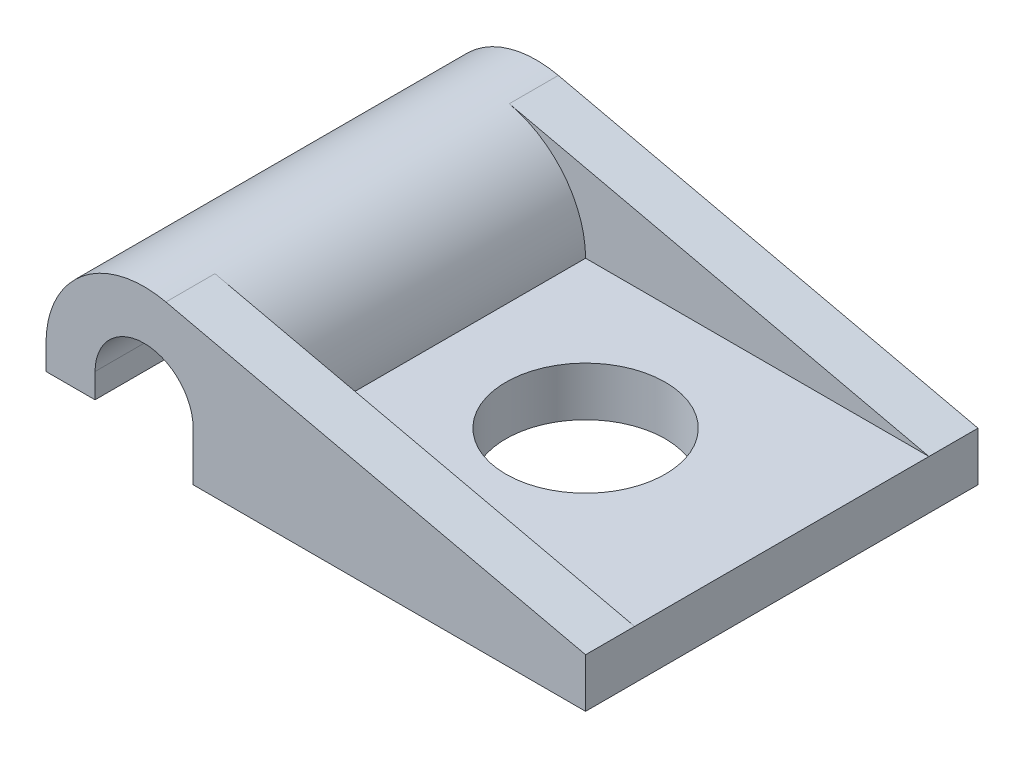
SolidWorks part; units mm, degrees
material "PVC 0.007 Plasticized"
ref_plane "Front" through (0, 0, 0) normal (0, 0, 1) x (1, 0, 0)
ref_plane "Top" through (0, 0, 0) normal (0, 1, 0) x (1, 0, 0)
ref_plane "Right" through (0, 0, 0) normal (1, 0, 0) x (0, 0, -1)
sketch "Sketch1" plane through (0, 0, 0) normal (0, 0, 1) x (1, 0, 0)
  line L11 (0, 14.2875) -> (0, 21.0796) construction
  line L12 (3.175, 1.5875) -> (3.175, 4.1203) construction
  line L13 (14.2875, 1.5875) -> (3.175, 1.5875) construction
  line L14 (-3.175, 0.7937) -> (-3.175, 1.5875)
  line L15 (-1.5875, 0.7937) -> (-3.175, 0.7937)
  line L16 (14.2875, 1.5875) -> (0.7056, 4.6831)
  line L17 (14.2875, 0) -> (14.2875, 1.5875)
  line L18 (1.5875, 0) -> (14.2875, 0)
  line L19 (1.5875, 1.5875) -> (1.5875, 0)
  line L20 (-1.5875, 1.5875) -> (-1.5875, 0.7937)
  arc A0 (1.5875, 1.5875) -> (-1.5875, 1.5875) centre (0, 1.5875) ccw
  arc A5 (-3.175, 1.5875) -> (0.7056, 4.6831) centre (0, 1.5875) cw
  point P2 (1.5181, 2.0516)
  point P13 (4.1275, 1.5875)
  point P41 (7.9375, 0)
  dimension "D1" = 0.7937
  dimension "ID" = 3.175
  dimension "Center to Center" = 7.9375
  dimension "Thickness" = 1.5875
extrude "Boss-Extrude1" add sketch "Sketch1" along normal mid plane 12.7
sketch "Sketch4" plane through (0, 0, 0) normal (0, 1, 0) x (1, 0, 0)
  line L1 (3.175, 4.7625) -> (14.2875, 4.7625)
  line L2 (3.175, 4.7625) -> (3.175, -4.7625)
  line L3 (3.175, -4.7625) -> (14.2875, -4.7625)
  line L4 (14.2875, 4.7625) -> (14.2875, -4.7625)
  line L7 (14.2875, -6.35) -> (14.2875, 6.35) construction
  line L8 (1.5875, 6.35) -> (14.2875, 6.35) construction
  point P6 (14.2875, 0)
  dimension "D1" = 1.5875
extrude "Cut-Extrude3" cut sketch "Sketch4" along normal through all from vertex at 1.5875 starting at point (14.2875, 1.5875, 0)
sketch "Sketch5" plane through (0, 0, 0) normal (0, 0, 1) x (1, 0, 0)
  line L0 (3.175, 1.5875) -> (3.175, 4.1203) construction
  line L1 (3.175, 1.5875) -> (3.175, 4.1203)
  line L3 (14.2875, 1.5875) -> (0.7056, 4.6831) construction
  line L4 (3.175, 4.1203) -> (0.7056, 4.6831)
  arc A1 (0.7056, 4.6831) -> (-3.175, 1.5875) centre (0, 1.5875) ccw construction
  arc A2 (3.175, 1.5875) -> (0.7056, 4.6831) centre (0, 1.5875) ccw
extrude "Cut-Extrude4" cut sketch "Sketch5" along normal up to surface and the other way up to surface up to face at (6.8792, 2.4318, 4.7625) other way up to face at (6.8792, 2.4318, -4.7625)
sketch "Sketch3" plane through (0, 0, 0) normal (0, 1, 0) x (1, 0, 0)
  circle A0 centre (7.9375, 0) radius 2.5797
  dimension "Mounting Hole Dia" = 5.1594
extrude "Cut-Extrude2" cut sketch "Sketch3" along normal blind 2.54
sketch "Sketch7" plane through (0, 0, 0) normal (0, 1, 0) x (1, 0, 0)
  line L0 (0, 6.985) -> (0, -6.985)
  line L2 (0.7056, 6.35) -> (-3.175, 6.35) construction
  dimension "D1" = 0.635
equation "\"D1@Sketch1\" = \"ID@Sketch1\" * .25"
equation "\"D1@Sketch4\" = \"Thickness@Sketch1\""
